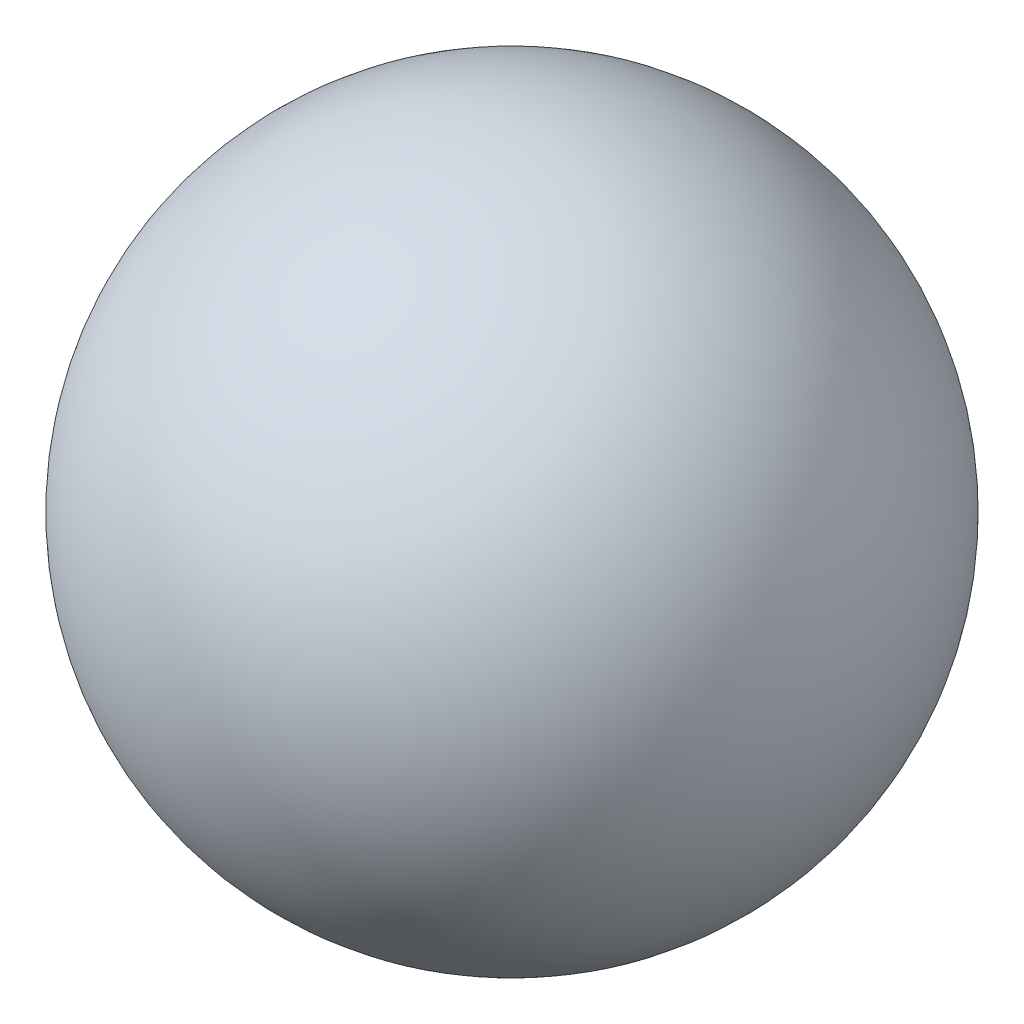
SolidWorks part; units mm, degrees
ref_plane "Przednia" through (0, 0, 0) normal (0, 0, 1) x (1, 0, 0)
ref_plane "Górna" through (0, 0, 0) normal (0, 1, 0) x (1, 0, 0)
ref_plane "Prawa" through (0, 0, 0) normal (1, 0, 0) x (0, 0, -1)
sketch "Szkic1" plane through (0, 0, 0) normal (0, 0, 1) x (1, 0, 0)
  line L0 (0, 0) -> (0, 8) construction
  line L1 (0, 8) -> (0, 0)
  arc A0 (0, 0) -> (0, 8) centre (0, 4) ccw
  dimension "D1" = 8
revolve "Obrót2" add sketch "Szkic1" angle 360 about L0
